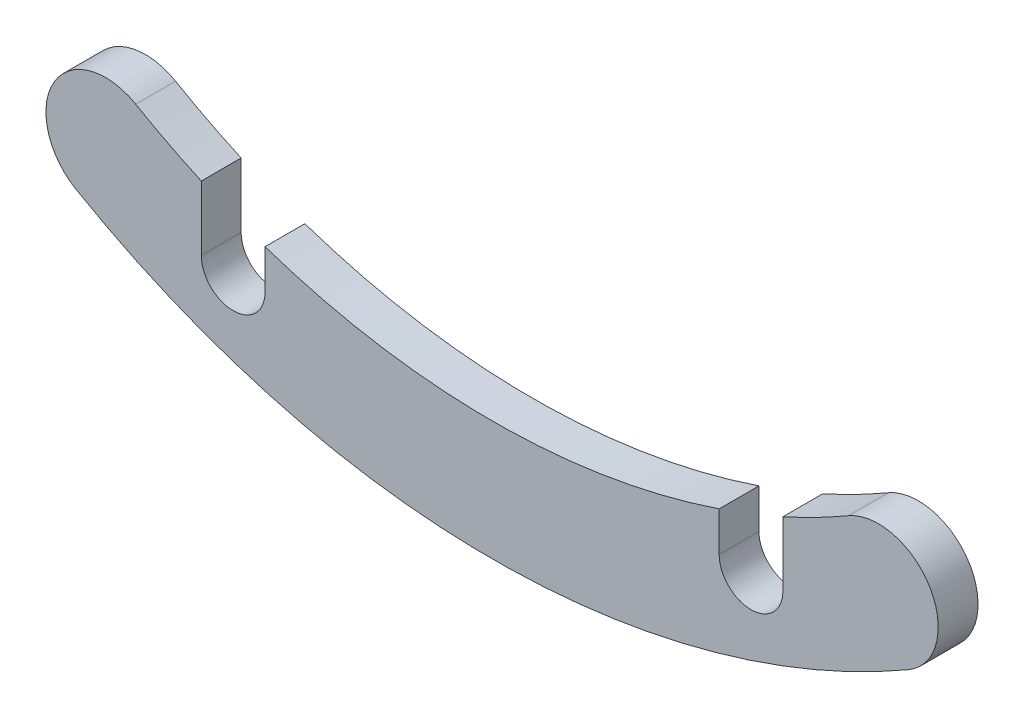
SolidWorks part; units mm, degrees
ref_plane "Front Plane" through (0, 0, 0) normal (0, 0, 1) x (1, 0, 0)
ref_plane "Top Plane" through (0, 0, 0) normal (0, 1, 0) x (1, 0, 0)
ref_plane "Right Plane" through (0, 0, 0) normal (1, 0, 0) x (0, 0, -1)
sketch "Sketch1" plane through (0, 0, 0) normal (0, 0, 1) x (1, 0, 0)
  line L0 (0, 0) -> (0, -20.8) construction
  arc A0 (-10.4539, -17.9821) -> (10.4539, -17.9821) centre (0, 0) ccw
  arc A1 (-8.9461, -15.3885) -> (8.9461, -15.3885) centre (0, 0) ccw
  arc A2 (-8.9461, -15.3885) -> (-10.4539, -17.9821) centre (-9.7, -16.6853) ccw
  circle A3 centre (0, 0) radius 17.8 construction
  circle A4 centre (0, 0) radius 20.8 construction
  arc A5 (8.9461, -15.3885) -> (10.4539, -17.9821) centre (9.7, -16.6853) cw
  point P2 (23.2257, 7.1008)
  point P8 (22.287, 0)
  dimension "D1" = 20.8
  dimension "D3" = 22.4
  dimension "D2" = 17.8
extrude "Boss-Extrude1" add sketch "Sketch1" against normal blind 1
sketch "Sketch2" plane through (0, 0, 0) normal (0, 0, 1) x (1, 0, 0)
  line L0 (0, 0) -> (0, -20.8) construction
  line L1 (-7.3, -17.8536) -> (-7.3, -16.2342)
  line L2 (-5.7, -17.8536) -> (-5.7, -16.8627)
  line L3 (5.7, -17.8536) -> (5.7, -16.8627)
  line L4 (7.3, -17.8536) -> (7.3, -16.2342)
  arc A0 (-10.4539, -17.9821) -> (10.4539, -17.9821) centre (0, 0) ccw construction
  circle A1 centre (0, 0) radius 19 construction
  arc A2 (-7.3, -17.8536) -> (-5.7, -17.8536) centre (-6.5, -17.8536) ccw
  arc A3 (-8.9461, -15.3885) -> (8.9461, -15.3885) centre (0, 0) ccw construction
  arc A4 (-7.3, -16.2342) -> (-5.7, -16.8627) centre (0, 0) ccw
  arc A5 (7.3, -17.8536) -> (5.7, -17.8536) centre (6.5, -17.8536) cw
  arc A6 (5.7, -16.8627) -> (7.3, -16.2342) centre (0, 0) ccw
  dimension "D1" = 0.8
  dimension "D3" = 38
  dimension "D2" = 13
extrude "Cut-Extrude1" cut sketch "Sketch2" against normal through all
